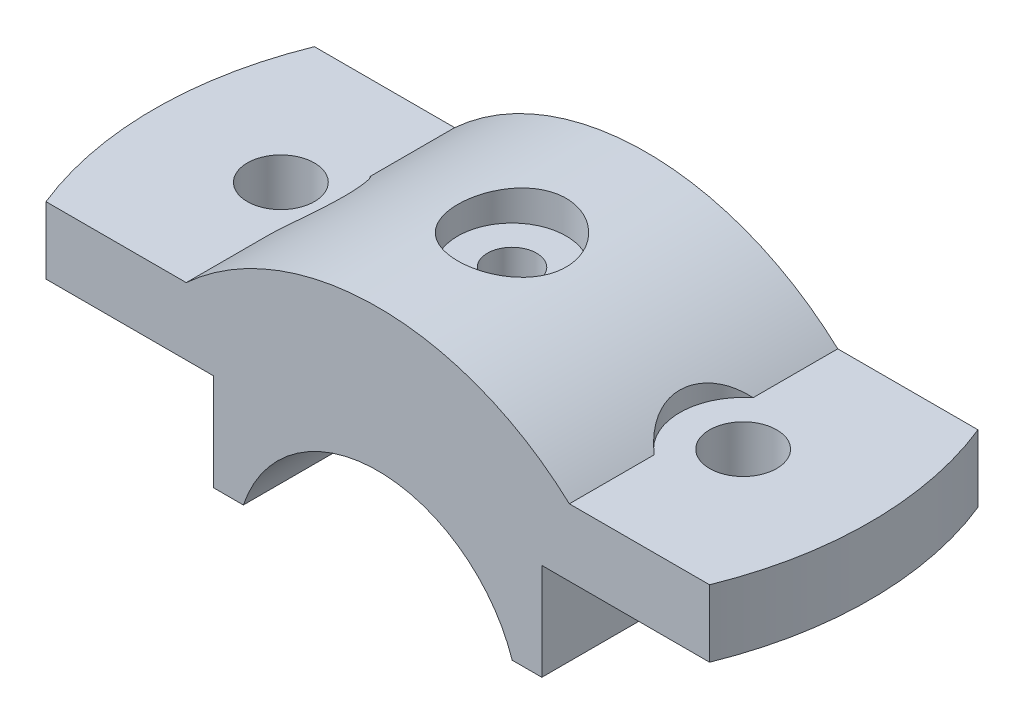
SolidWorks part; units mm, degrees
ref_plane "Front Plane" through (0, 0, 0) normal (0, 0, 1) x (1, 0, 0)
ref_plane "Top Plane" through (0, 0, 0) normal (0, 1, 0) x (1, 0, 0)
ref_plane "Right Plane" through (0, 0, 0) normal (1, 0, 0) x (0, 0, -1)
sketch "Sketch1" plane through (0, 0, 0) normal (0, 0, 1) x (1, 0, 0)
  line L0 (0, 78.6839) -> (0, -80.8274) construction
  line L1 (18.0278, 6) -> (22, 6)
  line L2 (22, 6) -> (22, 19)
  line L3 (22, 19) -> (50, 19)
  line L4 (50, 19) -> (50, 28)
  line L5 (50, 28) -> (29.3809, 28)
  line L6 (29.3809, 28) -> (25.6905, 28)
  line L9 (-29.3809, 28) -> (-25.6905, 28)
  line L10 (-50, 28) -> (-29.3809, 28)
  line L11 (-50, 19) -> (-50, 28)
  line L12 (-22, 19) -> (-50, 19)
  line L13 (-22, 6) -> (-22, 19)
  line L14 (-22, 6) -> (-18.0278, 6)
  arc A0 (18.0278, 6) -> (-18.0278, 6) centre (0, 0) ccw
  arc A1 (25.6905, 28) -> (-25.6905, 28) centre (0, 0) ccw
  dimension "D1" = 19
  dimension "D3" = 38
  dimension "D2" = 6
  dimension "D4" = 19
  dimension "D5" = 9
  dimension "D6" = 22
  dimension "D8" = 50
extrude "Boss-Extrude1" add sketch "Sketch1" along normal mid plane 36
sketch "Sketch4" plane through (0, 28, 0) normal (0, 1, 0) x (1, 0, 0)
  line L0 (-25.6905, 18) -> (-50, 18) construction
  line L1 (-25.6905, -18) -> (-50, -18) construction
  line L2 (-50, -18) -> (-50, 18) construction
  line L3 (-44.4972, 18) -> (-50, 18)
  line L4 (-50, -18) -> (-50, 18)
  line L5 (-44.4972, -18) -> (-50, -18)
  arc A0 (-44.4972, 18) -> (-44.4972, -18) centre (0, 0) ccw
  dimension "D1" = 48
extrude "Cut-Extrude1" cut sketch "Sketch4" against normal up to surface (9 mm away) up to face at (-36, 19, 0)
mirror "Mirror1" about plane through (0, 0, 0) normal (1, 0, 0) of "Cut-Extrude1"
sketch "Sketch5" plane through (0, 28, 0) normal (0, 1, 0) x (1, 0, 0)
  circle A0 centre (-31, 0) radius 4.5
  dimension "D1" = 9
  dimension "D2" = 31
extrude "Cut-Extrude2" cut sketch "Sketch5" against normal blind 10
sketch "Sketch7" plane through (0, 28, 0) normal (0, 1, 0) x (1, 0, 0)
  line L0 (-25.6905, -18) -> (-25.6905, 18) construction
  line L1 (-25.6905, -6.6377) -> (-25.6905, 6.6377)
  arc A0 (-25.6905, 6.6377) -> (-25.6905, -6.6377) centre (-31, 0) cw
  dimension "D1" = 8.5
extrude "Cut-Extrude3" cut sketch "Sketch7" along normal blind 10
mirror "Mirror2" about plane through (0, 0, 0) normal (1, 0, 0) of "Cut-Extrude2", "Cut-Extrude3"
hole_wizard "CBORE for M6 Hex Head Bolt4" positions "3DSketch6" profile "Sketch20" counterbore size "M6" standard "ANSI Metric" end condition through all
sketch3d "3DSketch6"
  point P0 (0, 38, 0)
sketch "Sketch20" plane through (0, 38, 0) normal (1, 0, 0) x (0, 0, 1)
  line L0 (0, 0) -> (0, 32)
  line L1 (0, 32) -> (3.3, 32)
  line L3 (3.3, 32) -> (3.3, 4.38)
  line L4 (3.3, 4.38) -> (7.275, 4.38)
  line L5 (7.275, 4.38) -> (7.275, 0)
  line L7 (7.275, 0) -> (0, 0)
  line L11 (0, -6.35) -> (0, 107.95) construction
  dimension "Thru Hole Dia." = 6.6
  dimension "Thru Hole Depth" = 32
  dimension "C'Bore Dia." = 14.55
  dimension "C'Bore Depth" = 4.38
